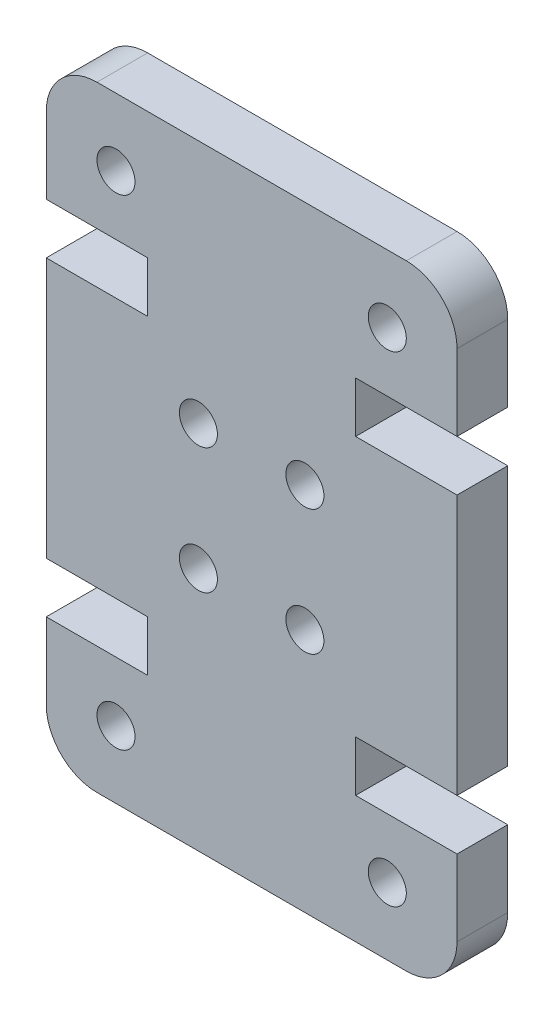
SolidWorks part; units mm, degrees
ref_plane "Front Plane" through (0, 0, 0) normal (0, 0, 1) x (1, 0, 0)
ref_plane "Top Plane" through (0, 0, 0) normal (0, 1, 0) x (1, 0, 0)
ref_plane "Right Plane" through (0, 0, 0) normal (1, 0, 0) x (0, 0, -1)
sketch "Sketch1" plane through (0, 0, 0) normal (0, 0, 1) x (1, 0, 0)
  line L0 (8.1, 24.26) -> (8.1, 0) construction
  line L1 (0, 12.13) -> (16.2, 12.13) construction
  line L2 (16.2, 17.26) -> (16.2, 7)
  line L3 (16.2, 2) -> (16.2, 5)
  line L4 (12.2, 5) -> (16.2, 5)
  line L5 (16.2, 7) -> (12.2, 7)
  line L6 (12.2, 7) -> (12.2, 5)
  line L7 (0, 22.26) -> (0, 19.26)
  line L8 (4, 19.26) -> (0, 19.26)
  line L9 (0, 17.26) -> (4, 17.26)
  line L10 (4, 17.26) -> (4, 19.26)
  line L11 (2, 24.26) -> (14.2, 24.26)
  line L12 (12.2, 17.26) -> (12.2, 19.26)
  line L13 (16.2, 17.26) -> (12.2, 17.26)
  line L14 (12.2, 19.26) -> (16.2, 19.26)
  line L15 (16.2, 22.26) -> (16.2, 19.26)
  line L21 (2, 0) -> (14.2, 0)
  line L25 (4, 7) -> (4, 5)
  line L28 (0, 7) -> (4, 7)
  line L30 (4, 5) -> (0, 5)
  line L34 (0, 2) -> (0, 5)
  line L38 (0, 17.26) -> (0, 7)
  circle A0 centre (13.45, 2.6536) radius 0.75
  circle A1 centre (10.2, 9.6536) radius 0.75
  arc A2 (16.2, 2) -> (14.2, 0) centre (14.2, 2) cw
  circle A3 centre (2.75, 21.6064) radius 0.75
  circle A4 centre (6, 14.6064) radius 0.75
  arc A5 (0, 22.26) -> (2, 24.26) centre (2, 22.26) cw
  arc A6 (16.2, 22.26) -> (14.2, 24.26) centre (14.2, 22.26) ccw
  circle A7 centre (10.2, 14.6064) radius 0.75
  circle A8 centre (13.45, 21.6064) radius 0.75
  arc A17 (0, 2) -> (2, 0) centre (2, 2) ccw
  circle A19 centre (6, 9.6536) radius 0.75
  circle A21 centre (2.75, 2.6536) radius 0.75
  point P16 (8.1, 12.13)
  dimension "D1" = 1.5
  dimension "D2" = 2
  dimension "D3" = 2.75
  dimension "D4" = 6
  dimension "D5" = 8.1
  dimension "D6" = 2.6536
  dimension "D7" = 5
  dimension "D9" = 9.6536
  dimension "D10" = 12.13
extrude "Boss-Extrude1" add sketch "Sketch1" along normal blind 2
equation "\"D5@Sketch1\"= \"fingerWidth@parametersSketch@prostheticParameters.SLDPRT\" / 2'PIP width"
equation "\"D10@Sketch1\"= ( \"HL@parametersSketch@prostheticParameters.SLDPRT\" * 0.196 - 4 - 8 ) / 2 'PIP length - Sil. Sht DIP - Sil. Sht PIP"
